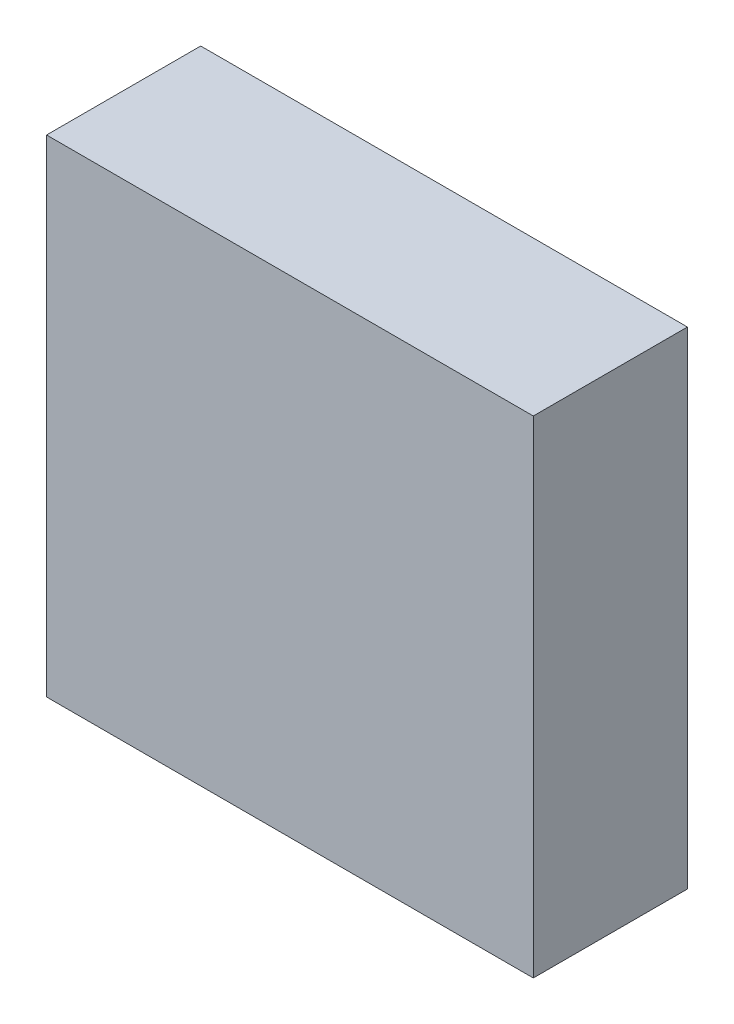
SolidWorks part; units mm, degrees
material "Pine"
ref_plane "Front Plane" through (0, 0, 0) normal (0, 0, 1) x (1, 0, 0)
ref_plane "Top Plane" through (0, 0, 0) normal (0, 1, 0) x (1, 0, 0)
ref_plane "Right Plane" through (0, 0, 0) normal (1, 0, 0) x (0, 0, -1)
sketch "Sketch1" plane through (0, 0, 0) normal (0, 0, 1) x (1, 0, 0)
  line L1 (0, 0) -> (15, 0)
  line L2 (0, 0) -> (0, 15)
  line L3 (0, 15) -> (15, 15)
  line L4 (15, 0) -> (15, 15)
  dimension "D1" = 15
extrude "Boss-Extrude1" add sketch "Sketch1" along normal blind 4.75
